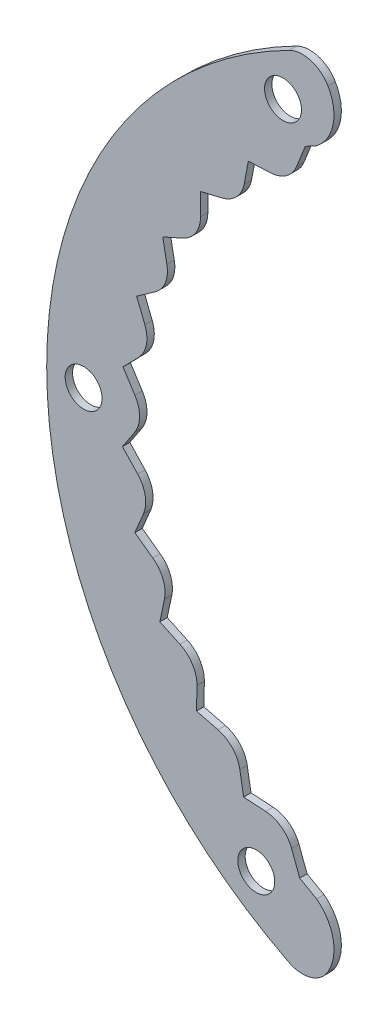
SolidWorks part; units mm, degrees
material "3003 Alaşım"
ref_plane "Ön Düzlem" through (0, 0, 0) normal (0, 0, 1) x (1, 0, 0)
ref_plane "Üst Düzlem" through (0, 0, 0) normal (0, 1, 0) x (1, 0, 0)
ref_plane "Sağ Düzlem" through (0, 0, 0) normal (1, 0, 0) x (0, 0, -1)
sketch "Çizim1" plane through (0, 0, 0) normal (0, 0, 1) x (1, 0, 0)
  line L0 (-50, 0) -> (-25, 0) construction
  line L1 (-25, 74.7114) -> (-25, -53.9079) construction
  line L2 (-23.4461, -44.162) -> (-25.7378, -42.8669)
  line L3 (-25, 43.3013) -> (-26.1465, 40.3921)
  line L10 (-32.6937, 37.73) -> (-33.2521, 34.7773)
  line L11 (-32.6937, 37.73) -> (-29.6915, 37.8626)
  line L12 (-39.1845, 30.9355) -> (-36.2603, 31.6283)
  line L13 (-39.1845, 30.9355) -> (-39.1797, 27.9304)
  line L14 (-44.2872, 23.0451) -> (-41.5446, 24.2736)
  line L15 (-44.2872, 23.0451) -> (-43.7194, 20.0942)
  line L16 (-47.8209, 14.3384) -> (-45.3571, 16.059)
  line L17 (-47.8209, 14.3384) -> (-46.7103, 11.546)
  line L18 (-49.6606, 5.1236) -> (-47.5629, 7.2754)
  line L19 (-49.6606, 5.1236) -> (-48.0464, 2.5889)
  line L20 (-49.7411, -4.2726) -> (-48.0837, -1.7658)
  line L21 (-49.7411, -4.2726) -> (-47.6805, -6.46)
  line L22 (-48.0594, -13.5175) -> (-46.9011, -10.7445)
  line L23 (-48.0594, -13.5175) -> (-45.6255, -15.28)
  line L24 (-44.6753, -22.2835) -> (-44.057, -19.3426)
  line L25 (-44.6753, -22.2835) -> (-41.9541, -23.5587)
  line L26 (-39.7084, -30.2601) -> (-39.6522, -27.2555)
  line L27 (-39.7084, -30.2601) -> (-36.7965, -31.0028)
  line L28 (-33.3349, -37.1647) -> (-33.8427, -34.2028)
  line L29 (-33.3349, -37.1647) -> (-30.3354, -37.3487)
  line L30 (-25.7378, -42.8669) -> (-26.8343, -39.9385)
  line L32 (-27.1796, -53.4909) -> (-27.1875, -53.4868)
  line L33 (-15, -47.697) -> (-15, -66.5436) construction
  line L35 (-25, -54.5436) -> (-25, -66.5436) construction
  arc A0 (-27.1796, 53.4909) -> (-27.1875, -53.4868) centre (0, 0) ccw
  arc A3 (-23.4461, 44.162) -> (-21.9062, 51.9296) centre (-27.0983, 48.9224) ccw
  arc A4 (-26.1465, 40.3921) -> (-29.6915, 37.8626) centre (-29.8679, 41.8587) cw
  arc A5 (-33.2521, 34.7773) -> (-36.2603, 31.6283) centre (-37.1824, 35.5206) cw
  arc A6 (-39.1797, 27.9304) -> (-41.5446, 24.2736) centre (-43.1797, 27.9241) cw
  arc A7 (-43.7194, 20.0942) -> (-45.3571, 16.059) centre (-47.6474, 19.3384) cw
  arc A8 (-46.7103, 11.546) -> (-47.5629, 7.2754) centre (-50.4271, 10.0677) cw
  arc A9 (-48.0464, 2.5889) -> (-48.0837, -1.7658) centre (-51.4203, 0.4403) cw
  arc A10 (-47.6805, -6.46) -> (-46.9011, -10.7445) centre (-50.592, -9.2028) cw
  arc A11 (-45.6255, -15.28) -> (-44.057, -19.3426) centre (-47.9715, -18.5198) cw
  arc A12 (-41.9541, -23.5587) -> (-39.6522, -27.2555) centre (-43.6515, -27.1807) cw
  arc A13 (-36.7965, -31.0028) -> (-33.8427, -34.2028) centre (-37.7852, -34.8787) cw
  arc A14 (-30.3354, -37.3487) -> (-26.8343, -39.9385) centre (-30.5803, -41.3412) cw
  arc A15 (-23.4461, 44.162) -> (-25, 43.3013) centre (0, 0) ccw
  arc A16 (-20.8333, 45.453) -> (-15, -47.697) centre (0, 0) ccw construction
  arc A19 (-25, 54.5436) -> (-25, -54.5436) centre (0, 0) ccw construction
  arc A21 (-27.1796, 53.4909) -> (-21.9062, 51.9296) centre (-25.3676, 49.9248) cw
  circle A26 centre (-31.6201, -45.0019) radius 2.5
  circle A27 centre (-55, 0) radius 2.5
  circle A28 centre (-28.0006, 47.3388) radius 2.5
  arc A30 (-23.4461, -44.162) -> (-21.9062, -51.9296) centre (-27.0983, -48.9224) cw
  arc A31 (-27.1796, -53.4909) -> (-21.9062, -51.9296) centre (-25.3676, -49.9248) ccw
  point P9 (-25, 0)
  point P69 (0, 0)
  dimension "D1" = 60
  dimension "D2" = 10
  dimension "D4" = 4
  dimension "D8" = 4
  dimension "D3" = 25
  dimension "D5" = 11
extrude "Yükseklik-Ekstrüzyon1" add sketch "Çizim1" along normal blind 1
scale "Scale1" scale about centroid uniform scaling yes scale factor 0.5
